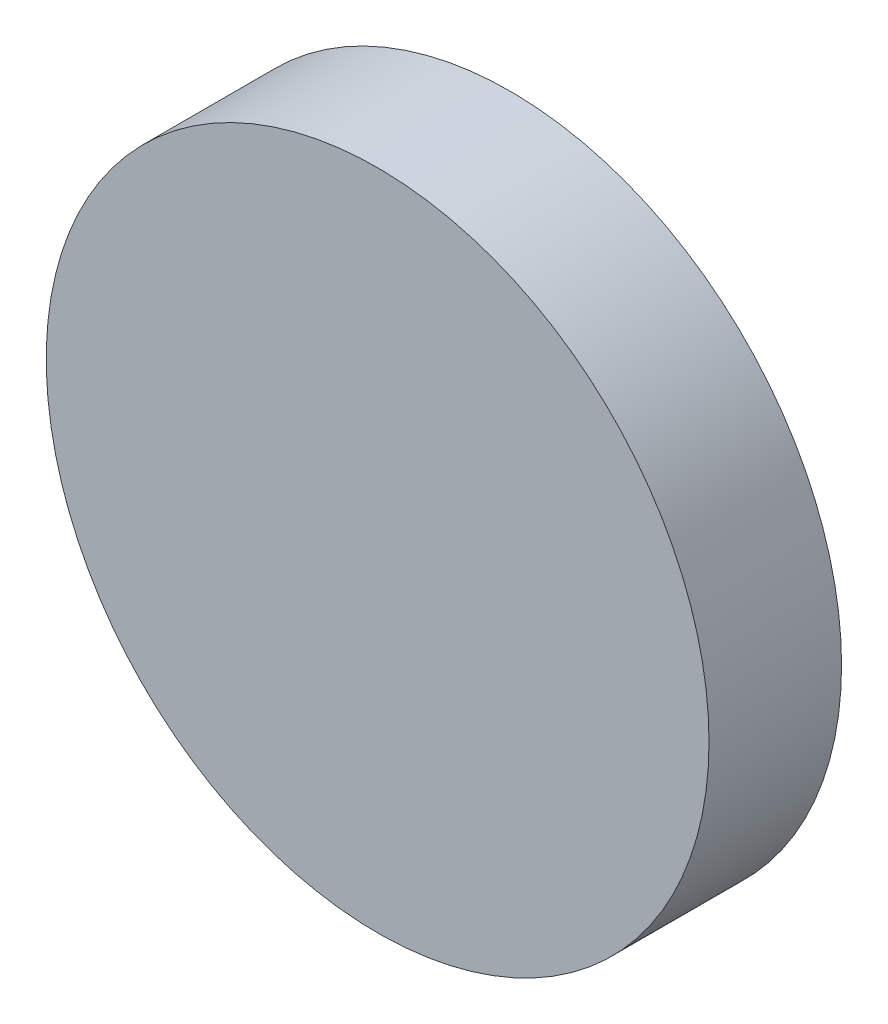
SolidWorks part; units mm, degrees
ref_plane "前视基准面" through (0, 0, 0) normal (0, 0, 1) x (1, 0, 0)
ref_plane "上视基准面" through (0, 0, 0) normal (0, 1, 0) x (1, 0, 0)
ref_plane "右视基准面" through (0, 0, 0) normal (1, 0, 0) x (0, 0, -1)
sketch "草图1" plane through (0, 0, 0) normal (0, 0, 1) x (1, 0, 0)
  circle A0 centre (0, 0) radius 12.5
  dimension "D1" = 25
extrude "凸台-拉伸1" add sketch "草图1" along normal blind 5 contours A0
